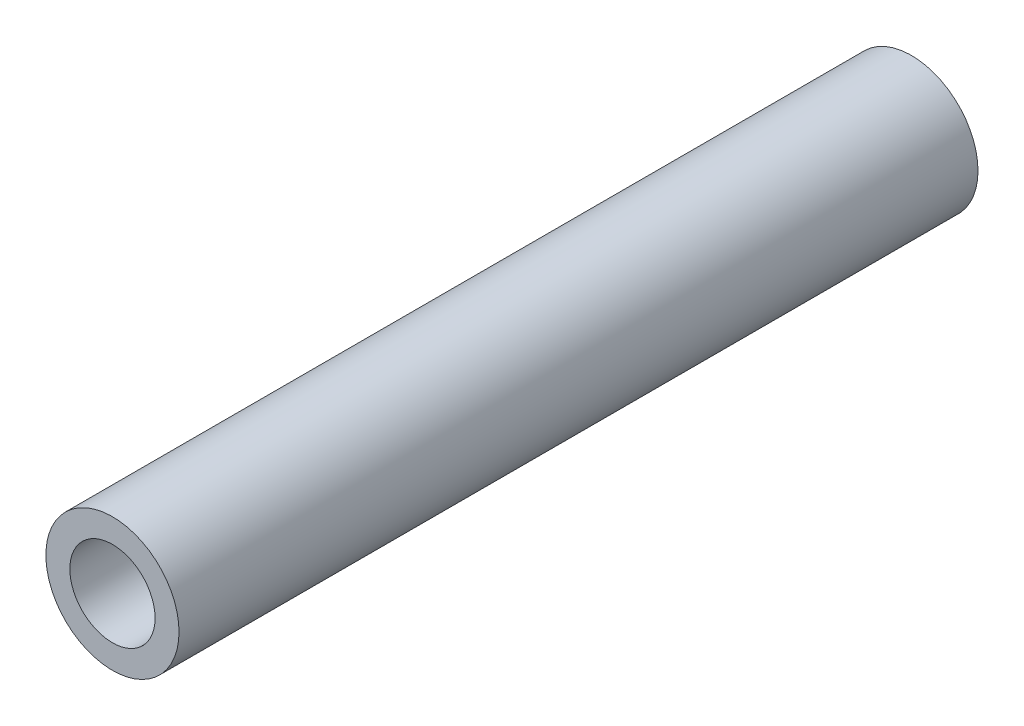
SolidWorks part; units mm, degrees
ref_plane "Front" through (0, 0, 0) normal (0, 0, 1) x (1, 0, 0)
ref_plane "Top" through (0, 0, 0) normal (0, 1, 0) x (1, 0, 0)
ref_plane "Right" through (0, 0, 0) normal (1, 0, 0) x (0, 0, -1)
sketch "Sketch1" plane through (0, 0, 0) normal (0, 0, 1) x (1, 0, 0)
  circle A0 centre (0, 0) radius 1.6
  circle A1 centre (0, 0) radius 2.5
extrude "Boss-Extrude4" add sketch "Sketch1" along normal blind 30
